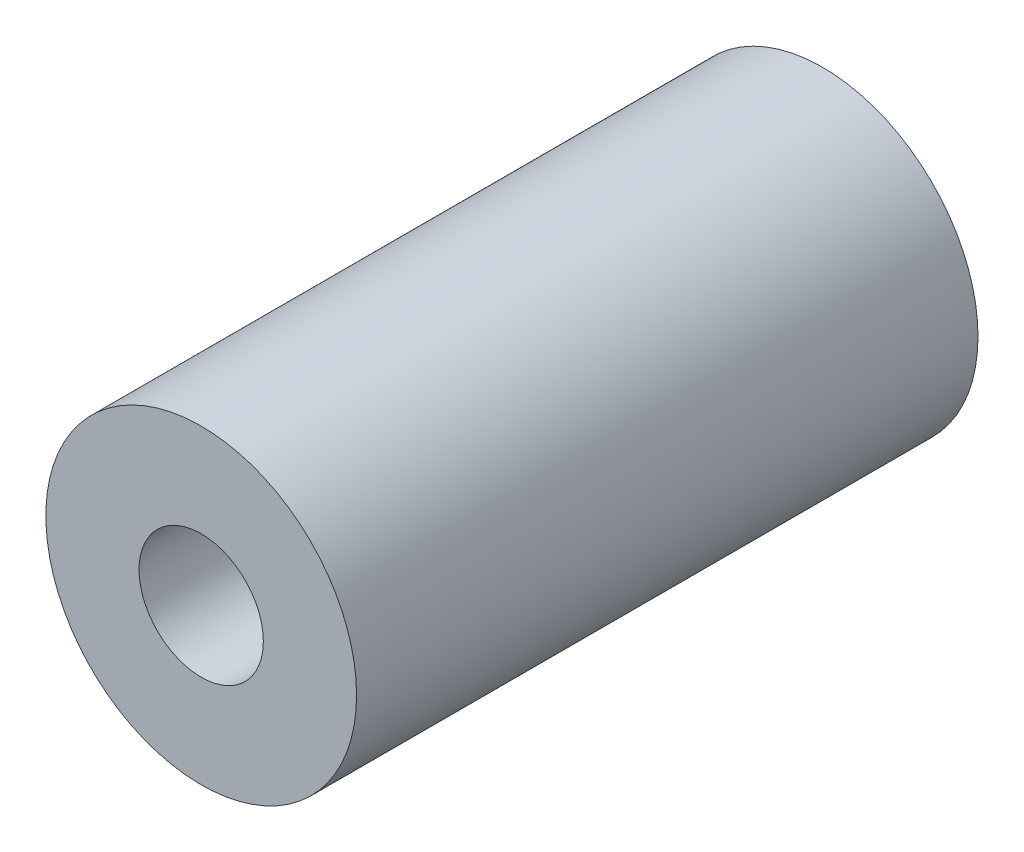
SolidWorks part; units mm, degrees
ref_plane "Ebene vorne" through (0, 0, 0) normal (0, 0, 1) x (1, 0, 0)
ref_plane "Ebene oben" through (0, 0, 0) normal (0, 1, 0) x (1, 0, 0)
ref_plane "Ebene rechts" through (0, 0, 0) normal (1, 0, 0) x (0, 0, -1)
sketch "Skizze1" plane through (0, 0, 0) normal (0, 0, 1) x (1, 0, 0)
  circle A0 centre (0, 0) radius 2.5
  circle A1 centre (0, 0) radius 1
  dimension "D1" = 2
  dimension "D2" = 5
extrude "Aufsatz-Linear austragen1" add sketch "Skizze1" against normal blind 10
